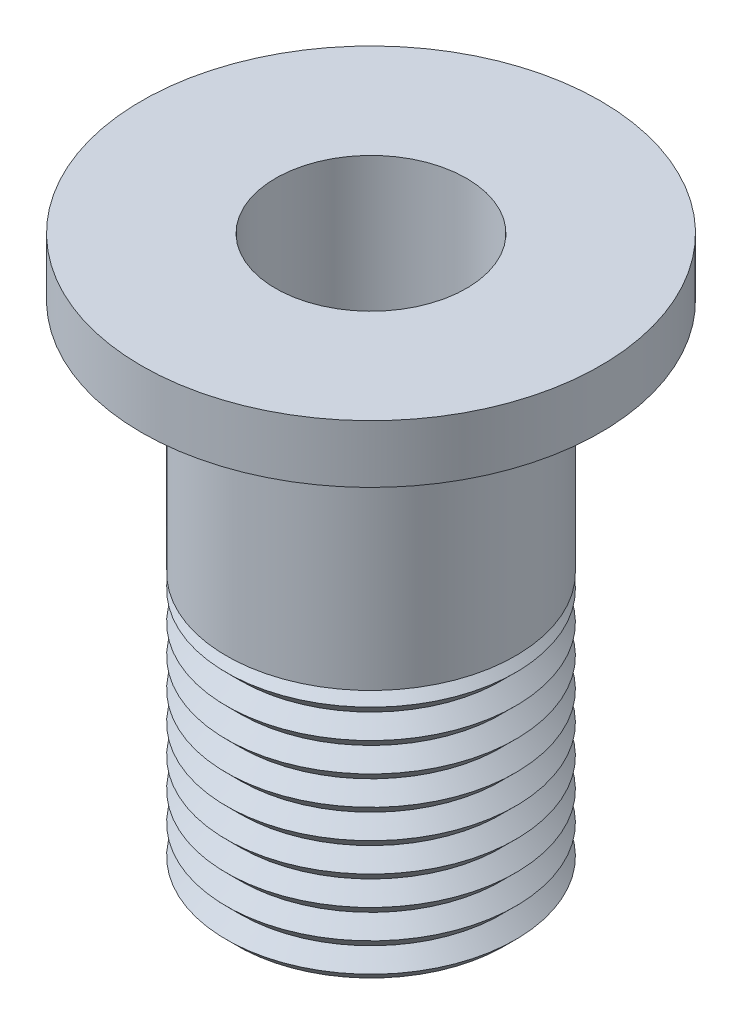
SolidWorks part; units mm, degrees
material "Polyetheretherketone (PEEK)"
ref_plane "Front Plane" through (0, 0, 0) normal (0, 0, 1) x (1, 0, 0)
ref_plane "Top Plane" through (0, 0, 0) normal (0, 1, 0) x (1, 0, 0)
ref_plane "Right Plane" through (0, 0, 0) normal (1, 0, 0) x (0, 0, -1)
sketch "Sketch1" plane through (0, 0, 0) normal (0, 0, 1) x (1, 0, 0)
  line L0 (0, 0) -> (0, 42.8538) construction
  line L1 (3.302, 0) -> (3.302, 19.05)
  line L2 (3.302, 19.05) -> (7.9375, 19.05)
  line L3 (7.9375, 19.05) -> (7.9375, 17.05)
  line L4 (7.9375, 17.05) -> (5, 17.05)
  line L5 (5, 17.05) -> (5, 8.89)
  line L6 (5, 8.89) -> (4.5, 8.89)
  line L7 (4.5, 8.89) -> (4.5, 0) construction
  line L8 (4.61, 0) -> (3.302, 0)
  line L9 (4.5, 8.89) -> (5, 8.39)
  line L10 (5, 8.39) -> (4.5, 7.89)
  line L11 (5, 8.89) -> (5, -0.5195) construction
  line L12 (4.5, 7.89) -> (5, 7.39)
  line L13 (5, 7.39) -> (4.5, 6.89)
  line L14 (4.5, 6.89) -> (5, 6.39)
  line L15 (5, 6.39) -> (4.5, 5.89)
  line L16 (4.5, 5.89) -> (5, 5.39)
  line L17 (5, 5.39) -> (4.5, 4.89)
  line L18 (4.5, 4.89) -> (5, 4.39)
  line L19 (5, 4.39) -> (4.5, 3.89)
  line L20 (4.5, 3.89) -> (5, 3.39)
  line L21 (5, 3.39) -> (4.5, 2.89)
  line L22 (4.5, 2.89) -> (5, 2.39)
  line L23 (5, 2.39) -> (4.5, 1.89)
  line L24 (4.5, 1.89) -> (5, 1.39)
  line L25 (5, 1.39) -> (4.5, 0.89)
  line L26 (4.5, 0.89) -> (5, 0.39)
  line L27 (5, 0.39) -> (4.61, 0)
  dimension "D1" = 6.604
  dimension "D2" = 15.875
  dimension "D3" = 2
  dimension "D4" = 19.05
  dimension "D5" = 8.89
  dimension "D6" = 10
  dimension "D7" = 4.5
  dimension "D8" = 1
  dimension "D9" = 0.5
revolve "Revolve1" add sketch "Sketch1" angle 360 about L0
